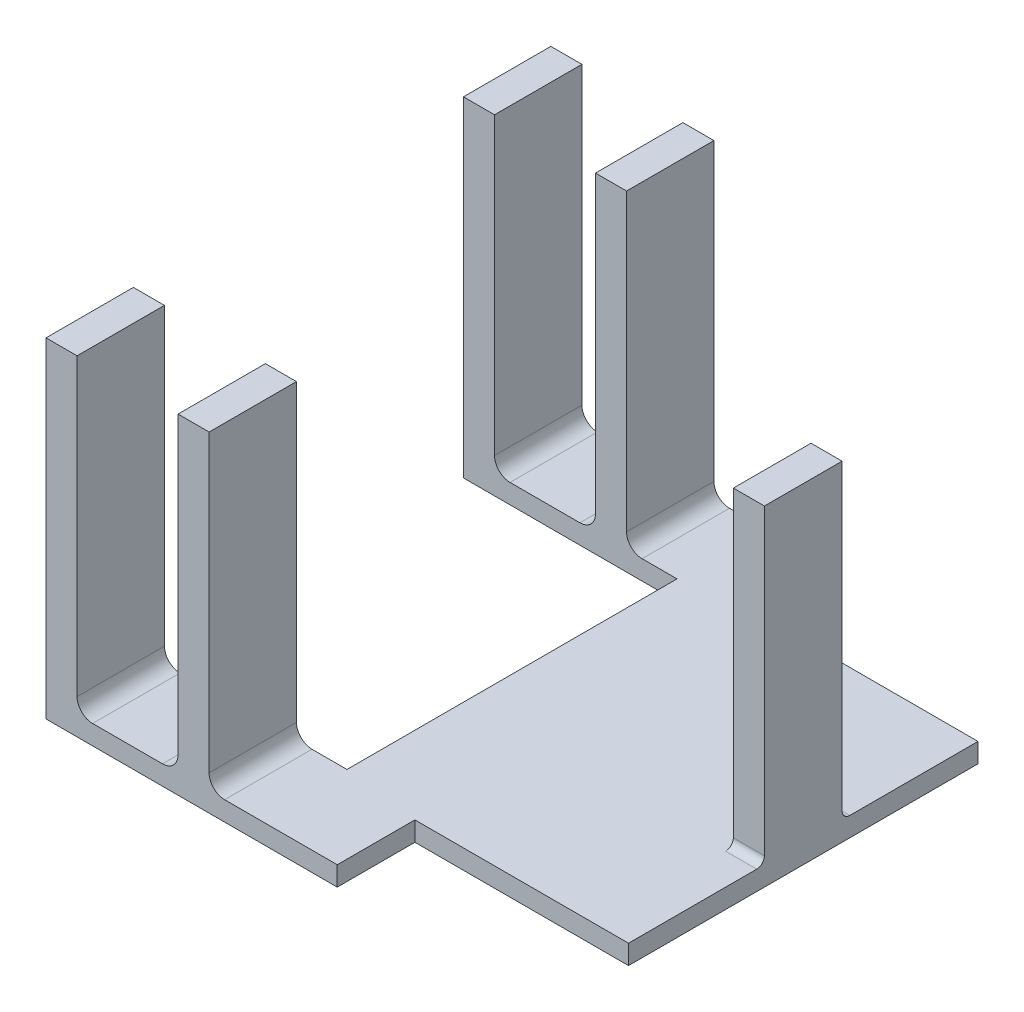
SolidWorks part; units mm, degrees
ref_plane "Front Plane" through (0, 0, 0) normal (0, 0, 1) x (1, 0, 0)
ref_plane "Top Plane" through (0, 0, 0) normal (0, 1, 0) x (1, 0, 0)
ref_plane "Right Plane" through (0, 0, 0) normal (1, 0, 0) x (0, 0, -1)
sketch "Sketch1" plane through (0, 0, 0) normal (0, 1, 0) x (1, 0, 0)
  line L0 (0, 114.3) -> (0, 139.7)
  line L1 (0, 0) -> (69.85, 0)
  line L3 (0, 114.3) -> (69.85, 114.3)
  line L4 (69.85, 0) -> (69.85, 114.3)
  line L5 (0, 139.7) -> (-95.25, 139.7)
  line L6 (-95.25, 139.7) -> (-95.25, 111.125)
  line L7 (-95.25, 111.125) -> (-25.4, 111.125)
  line L8 (-25.4, 111.125) -> (-25.4, 3.175)
  line L10 (-95.25, 3.175) -> (-25.4, 3.175)
  line L11 (0, -25.4) -> (-95.25, -25.4)
  line L12 (-95.25, -25.4) -> (-95.25, 3.175)
  line L13 (0, -25.4) -> (0, 0)
  dimension "D1" = 69.85
  dimension "D2" = 114.3
  dimension "D3" = 25.4
  dimension "D4" = 95.25
  dimension "D5" = 28.575
extrude "Boss-Extrude1" add sketch "Sketch1" along normal blind 6.35
sketch "Sketch4" plane through (0, 6.35, 0) normal (0, 1, 0) x (1, 0, 0)
  line L0 (-95.25, -25.4) -> (0, -25.4) construction
  line L1 (-95.25, 3.175) -> (-85.09, 3.175)
  line L2 (-95.25, 3.175) -> (-95.25, -25.4)
  line L3 (-95.25, -25.4) -> (-85.09, -25.4)
  line L4 (-85.09, 3.175) -> (-85.09, -25.4)
  line L5 (-25.4, 3.175) -> (-95.25, 3.175) construction
  line L6 (-52.07, -25.4) -> (-41.91, -25.4)
  line L7 (-52.07, -25.4) -> (-52.07, 3.175)
  line L8 (-52.07, 3.175) -> (-41.91, 3.175)
  line L9 (-41.91, -25.4) -> (-41.91, 3.175)
  dimension "D1" = 10.16
  dimension "D2" = 10.16
  dimension "D3" = 33.02
extrude "Boss-Extrude4" add sketch "Sketch4" along normal blind 101.6
sketch "Sketch5" plane through (0, 6.35, 0) normal (0, 1, 0) x (1, 0, 0)
  line L0 (-95.25, 111.125) -> (-25.4, 111.125) construction
  line L1 (-95.25, 139.7) -> (-85.09, 139.7)
  line L2 (-95.25, 139.7) -> (-95.25, 111.125)
  line L3 (-95.25, 111.125) -> (-85.09, 111.125)
  line L4 (-85.09, 139.7) -> (-85.09, 111.125)
  line L5 (0, 139.7) -> (-95.25, 139.7) construction
  line L6 (-41.91, 139.7) -> (-52.07, 139.7)
  line L7 (-41.91, 139.7) -> (-41.91, 111.125)
  line L8 (-41.91, 111.125) -> (-52.07, 111.125)
  line L9 (-52.07, 139.7) -> (-52.07, 111.125)
  dimension "D1" = 10.16
  dimension "D2" = 33.02
  dimension "D3" = 10.16
extrude "Boss-Extrude5" add sketch "Sketch5" along normal blind 101.6
sketch "Sketch6" plane through (0, 6.35, 0) normal (0, 1, 0) x (1, 0, 0)
  line L0 (69.85, 0) -> (69.85, 114.3) construction
  line L1 (69.85, 44.45) -> (59.69, 44.45)
  line L2 (69.85, 44.45) -> (69.85, 69.85)
  line L3 (69.85, 69.85) -> (59.69, 69.85)
  line L4 (59.69, 44.45) -> (59.69, 69.85)
  line L5 (0, 0) -> (69.85, 0) construction
  point P6 (64.77, 44.45)
  dimension "D1" = 10.16
  dimension "D2" = 25.4
  dimension "D3" = 44.45
extrude "Boss-Extrude7" add sketch "Sketch6" along normal blind 101.6 contours L4 L3 L2 L1
fillet "Fillet2" radius 5.08 1 edges at (-41.91, 6.35, 11.1125)
fillet "Fillet3" radius 5.08 1 edges at (-52.07, 6.35, 11.1125)
fillet "Fillet4" radius 5.08 1 edges at (-85.09, 6.35, 11.1125)
fillet "Fillet5" radius 5.08 1 edges at (-85.09, 6.35, -125.4125)
fillet "Fillet6" radius 5.08 1 edges at (-52.07, 6.35, -125.4125)
fillet "Fillet7" radius 5.08 1 edges at (-41.91, 6.35, -125.4125)
fillet "Fillet8" radius 2.54 1 edges at (64.77, 6.35, -44.45)
fillet "Fillet9" radius 2.54 1 edges at (64.77, 6.35, -69.85)
